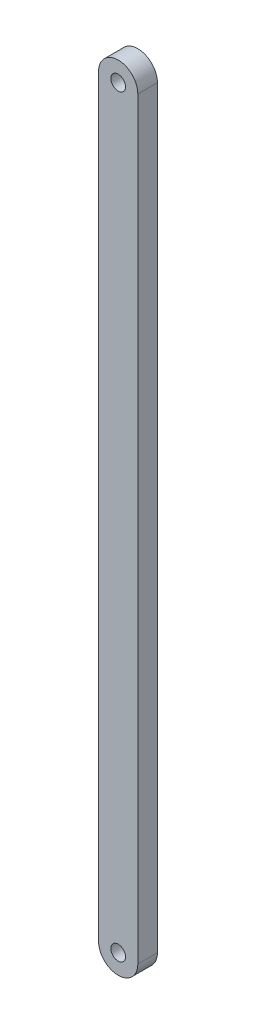
SolidWorks part; units mm, degrees
ref_plane "Front Plane" through (0, 0, 0) normal (0, 0, 1) x (1, 0, 0)
ref_plane "Top Plane" through (0, 0, 0) normal (0, 1, 0) x (1, 0, 0)
ref_plane "Right Plane" through (0, 0, 0) normal (1, 0, 0) x (0, 0, -1)
sketch "Sketch1" plane through (0, 0, 0) normal (0, 0, 1) x (1, 0, 0)
  line L0 (0, 243.84) -> (0, -243.84) construction
  line L1 (12.7, 243.84) -> (12.7, -243.84)
  line L2 (-12.7, 243.84) -> (-12.7, -243.84)
  arc A0 (12.7, 243.84) -> (-12.7, 243.84) centre (0, 243.84) ccw
  arc A1 (-12.7, -243.84) -> (12.7, -243.84) centre (0, -243.84) ccw
  circle A2 centre (0, 243.84) radius 4.7625
  circle A3 centre (0, -243.84) radius 4.7625
  point P3 (0, 0)
  dimension "D2" = 9.525
  dimension "D1" = 487.68
  dimension "D3" = 25.4
extrude "Boss-Extrude1" add sketch "Sketch1" along normal blind 12.7
